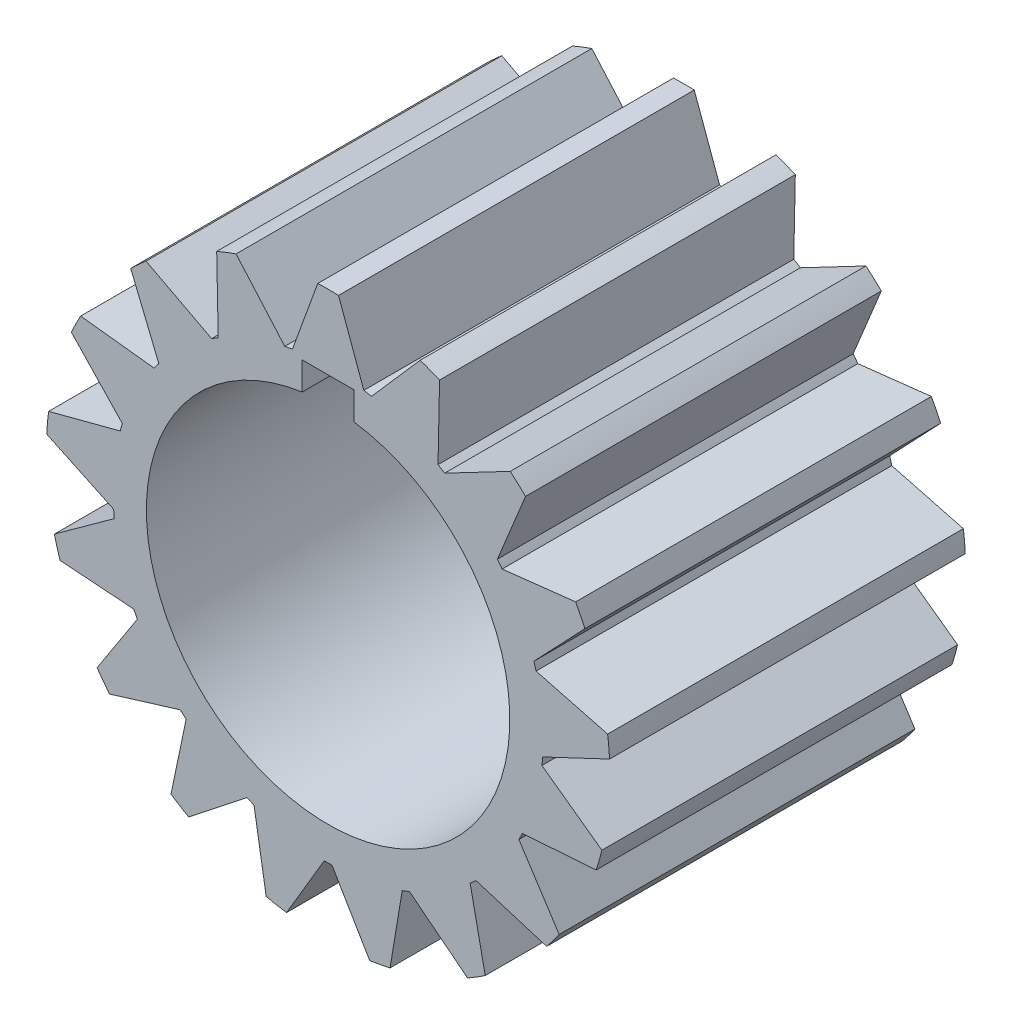
SolidWorks part; units mm, degrees
ref_plane "Front Plane" through (0, 0, 0) normal (0, 0, 1) x (1, 0, 0)
ref_plane "Top Plane" through (0, 0, 0) normal (0, 1, 0) x (1, 0, 0)
ref_plane "Right Plane" through (0, 0, 0) normal (1, 0, 0) x (0, 0, -1)
sketch "Sketch2" plane through (0, 0, 0) normal (0, 0, 1) x (1, 0, 0)
  line L0 (-4.366, 25.9419) -> (-1.27, 34.4482)
  line L1 (1.27, 34.4482) -> (4.366, 25.9419)
  line L2 (0, 0) -> (0, 34.4716) construction
  line L3 (5.3001, 25.7673) -> (11.2599, 32.5808)
  line L4 (13.6284, 31.6632) -> (13.4425, 22.613)
  line L5 (14.2504, 22.1127) -> (22.2691, 26.3131)
  line L6 (24.1461, 24.6019) -> (20.7035, 16.23)
  line L7 (21.2762, 15.4716) -> (30.2707, 16.4917)
  line L8 (31.4029, 14.218) -> (25.1684, 7.655)
  line L9 (25.4284, 6.741) -> (34.1841, 4.4431)
  line L10 (34.4184, 1.9139) -> (26.2341, -1.9538)
  line L11 (26.1464, -2.9) -> (33.4807, -8.2057)
  line L12 (32.7856, -10.6487) -> (23.7568, -11.2987)
  line L13 (23.3332, -12.1493) -> (28.2556, -19.7462)
  line L14 (26.7249, -21.7732) -> (18.071, -19.1177)
  line L15 (17.3687, -19.7579) -> (19.2144, -28.6199)
  line L16 (17.0549, -29.957) -> (9.9446, -24.3547)
  line L17 (9.0585, -24.698) -> (7.5782, -33.6283)
  line L18 (5.0815, -34.095) -> (0.4751, -26.3025)
  line L19 (-0.4751, -26.3025) -> (-5.0815, -34.095)
  line L20 (-7.5782, -33.6283) -> (-9.0585, -24.698)
  line L21 (-9.9446, -24.3547) -> (-17.0549, -29.957)
  line L22 (-19.2144, -28.6199) -> (-17.3687, -19.7579)
  line L23 (-18.071, -19.1177) -> (-26.7249, -21.7732)
  line L24 (-28.2556, -19.7462) -> (-23.3332, -12.1493)
  line L25 (-23.7568, -11.2987) -> (-32.7856, -10.6487)
  line L26 (-33.4807, -8.2057) -> (-26.1464, -2.9)
  line L27 (-26.2341, -1.9538) -> (-34.4184, 1.9139)
  line L28 (-34.1841, 4.4431) -> (-25.4284, 6.741)
  line L29 (-25.1684, 7.655) -> (-31.4029, 14.218)
  line L30 (-30.2707, 16.4917) -> (-21.2762, 15.4716)
  line L31 (-20.7035, 16.23) -> (-24.1461, 24.6019)
  line L32 (-22.2691, 26.3131) -> (-14.2504, 22.1127)
  line L33 (-13.4425, 22.613) -> (-13.6284, 31.6632)
  line L34 (-11.2599, 32.5808) -> (-5.3001, 25.7673)
  arc A0 (-4.366, 25.9419) -> (-5.3001, 25.7673) centre (0, 0) ccw
  arc A1 (1.27, 34.4482) -> (-1.27, 34.4482) centre (0, 0) ccw
  arc A2 (13.6284, 31.6632) -> (11.2599, 32.5808) centre (0, 0) ccw
  arc A3 (24.1461, 24.6019) -> (22.2691, 26.3131) centre (0, 0) ccw
  arc A4 (31.4029, 14.218) -> (30.2707, 16.4917) centre (0, 0) ccw
  arc A5 (34.4184, 1.9139) -> (34.1841, 4.4431) centre (0, 0) ccw
  arc A6 (32.7856, -10.6487) -> (33.4807, -8.2057) centre (0, 0) ccw
  arc A7 (26.7249, -21.7732) -> (28.2556, -19.7462) centre (0, 0) ccw
  arc A8 (17.0549, -29.957) -> (19.2144, -28.6199) centre (0, 0) ccw
  arc A9 (5.0815, -34.095) -> (7.5782, -33.6283) centre (0, 0) ccw
  arc A10 (-7.5782, -33.6283) -> (-5.0815, -34.095) centre (0, 0) ccw
  arc A11 (-19.2144, -28.6199) -> (-17.0549, -29.957) centre (0, 0) ccw
  arc A12 (-28.2556, -19.7462) -> (-26.7249, -21.7732) centre (0, 0) ccw
  arc A13 (-33.4807, -8.2057) -> (-32.7856, -10.6487) centre (0, 0) ccw
  arc A14 (-34.1841, 4.4431) -> (-34.4184, 1.9139) centre (0, 0) ccw
  arc A15 (-30.2707, 16.4917) -> (-31.4029, 14.218) centre (0, 0) ccw
  arc A16 (-22.2691, 26.3131) -> (-24.1461, 24.6019) centre (0, 0) ccw
  arc A17 (-11.2599, 32.5808) -> (-13.6284, 31.6632) centre (0, 0) ccw
  arc A18 (-13.4425, 22.613) -> (-14.2504, 22.1127) centre (0, 0) ccw
  arc A19 (-20.7035, 16.23) -> (-21.2762, 15.4716) centre (0, 0) ccw
  arc A20 (-25.1684, 7.655) -> (-25.4284, 6.741) centre (0, 0) ccw
  arc A21 (-26.2341, -1.9538) -> (-26.1464, -2.9) centre (0, 0) ccw
  arc A22 (-23.7568, -11.2987) -> (-23.3332, -12.1493) centre (0, 0) ccw
  arc A23 (-18.071, -19.1177) -> (-17.3687, -19.7579) centre (0, 0) ccw
  arc A24 (-9.9446, -24.3547) -> (-9.0585, -24.698) centre (0, 0) ccw
  arc A25 (-0.4751, -26.3025) -> (0.4751, -26.3025) centre (0, 0) ccw
  arc A26 (9.0585, -24.698) -> (9.9446, -24.3547) centre (0, 0) ccw
  arc A27 (17.3687, -19.7579) -> (18.071, -19.1177) centre (0, 0) ccw
  arc A28 (23.3332, -12.1493) -> (23.7568, -11.2987) centre (0, 0) ccw
  arc A29 (26.1464, -2.9) -> (26.2341, -1.9538) centre (0, 0) ccw
  arc A30 (25.4284, 6.741) -> (25.1684, 7.655) centre (0, 0) ccw
  arc A31 (21.2762, 15.4716) -> (20.7035, 16.23) centre (0, 0) ccw
  arc A32 (14.2504, 22.1127) -> (13.4425, 22.613) centre (0, 0) ccw
  arc A33 (5.3001, 25.7673) -> (4.366, 25.9419) centre (0, 0) ccw
  point P75 (0, 0)
  dimension "D1" = 52.6136
  dimension "D2" = 68.9432
  dimension "D3" = 1.27
  dimension "D4" = 1.27
  dimension "D5" = 20
  dimension "D6" = 20
  dimension "D7" = 17
extrude "Boss-Extrude1" add sketch "Sketch2" along normal blind 43.5102
sketch "Sketch4" plane through (0, 0, 43.5102) normal (0, 0, 1) x (1, 0, 0)
  line L0 (0, 0) -> (0, 22.225) construction
  line L1 (-3.175, 25.4) -> (3.175, 25.4)
  line L2 (-3.175, 25.4) -> (-3.175, 21.997)
  line L4 (3.175, 25.4) -> (3.175, 21.997)
  line L5 (3.175, 22.225) -> (5.6842, 22.225) construction
  line L6 (0, 25.4) -> (0, 29.3306) construction
  arc A0 (-3.175, 21.997) -> (3.175, 21.997) centre (0, 0) ccw
  point P7 (0, 25.4)
  dimension "D1" = 44.45
  dimension "D2" = 3.175
  dimension "D3" = 6.35
extrude "Cut-Extrude1" cut sketch "Sketch4" against normal up to surface (43.5102 mm away) up to face at (0, 0, 0)
